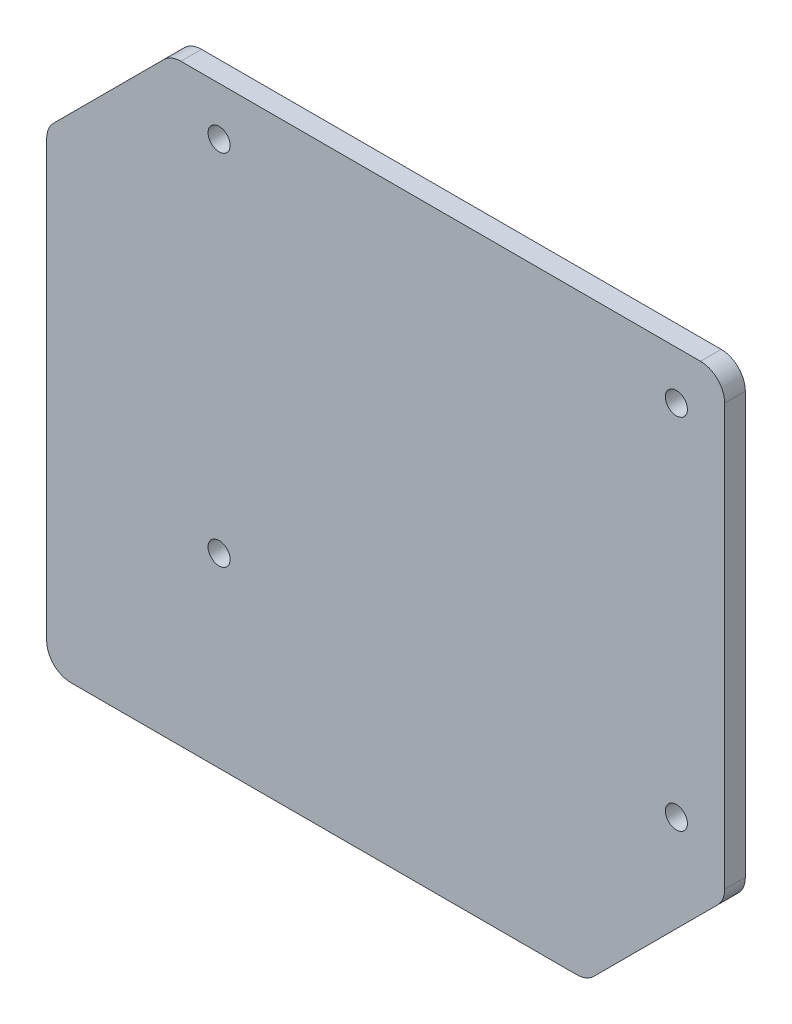
SolidWorks part; units mm, degrees
material "Acrylic (Medium-high impact)"
ref_plane "Front Plane" through (0, 0, 0) normal (0, 0, 1) x (1, 0, 0)
ref_plane "Top Plane" through (0, 0, 0) normal (0, 1, 0) x (1, 0, 0)
ref_plane "Right Plane" through (0, 0, 0) normal (1, 0, 0) x (0, 0, -1)
sketch "Sketch1" plane through (0, 0, 0) normal (0, 0, 1) x (1, 0, 0)
  line L0 (0, 66) -> (-18, 48)
  line L1 (0, 0) -> (80.3, 0)
  line L2 (0, 0) -> (0, 66)
  line L3 (0, 66) -> (80.3, 66)
  line L4 (80.3, 0) -> (80.3, 66)
  line L5 (-18, 48) -> (-18, -20)
  line L6 (-18, -20) -> (60.3, -20)
  line L7 (60.3, -20) -> (80.3, 0)
  dimension "D1" = 80.3
  dimension "D2" = 66
  dimension "D3" = 20
  dimension "D4" = 18
  dimension "D5" = 45
  dimension "D6" = 45
extrude "Boss-Extrude1" add sketch "Sketch1" along normal blind 3 contours L6 L7 L1 L2 L0 L5 | L1 L4 L3 L2
fillet "Fillet1" radius 3.5 6 edges at (80.3, 0, 1.5) (60.3, -20, 1.5) (-18, -20, 1.5) (-18, 48, 1.5) (80.3, 66, 1.5) (0, 66, 1.5)
hole_wizard "Ø3.2 (3.2) Diameter Hole1" positions "Sketch5" profile "Sketch6" hole size "Ø3.2" standard "ANSI Metric" end condition through all
sketch "Sketch5" plane through (0, 0, 3) normal (0, 0, 1) x (1, 0, 0)
  line L5 (80.3, 1.4497) -> (80.3, 62.5) construction
  line L7 (1.4497, 66) -> (76.8, 66) construction
  point P0 (7, 59)
  point P2 (73.3, 59)
  point P4 (73.3, 7)
  point P6 (7, 7)
  dimension "D1" = 7
  dimension "D2" = 7
  dimension "D3" = 66.3
  dimension "D4" = 52
sketch "Sketch6" plane through (7, 59, 3) normal (1, 0, 0) x (0, -1, 0)
  line L0 (0, 0) -> (0, 3)
  line L1 (0, 3) -> (1.6, 3)
  line L2 (1.6, 3) -> (1.6, 0)
  line L5 (1.6, 0) -> (0, 0)
  line L11 (0, -6.35) -> (0, 107.95) construction
  dimension "Thru Hole Dia." = 3.2
  dimension "Thru Hole Depth" = 3
